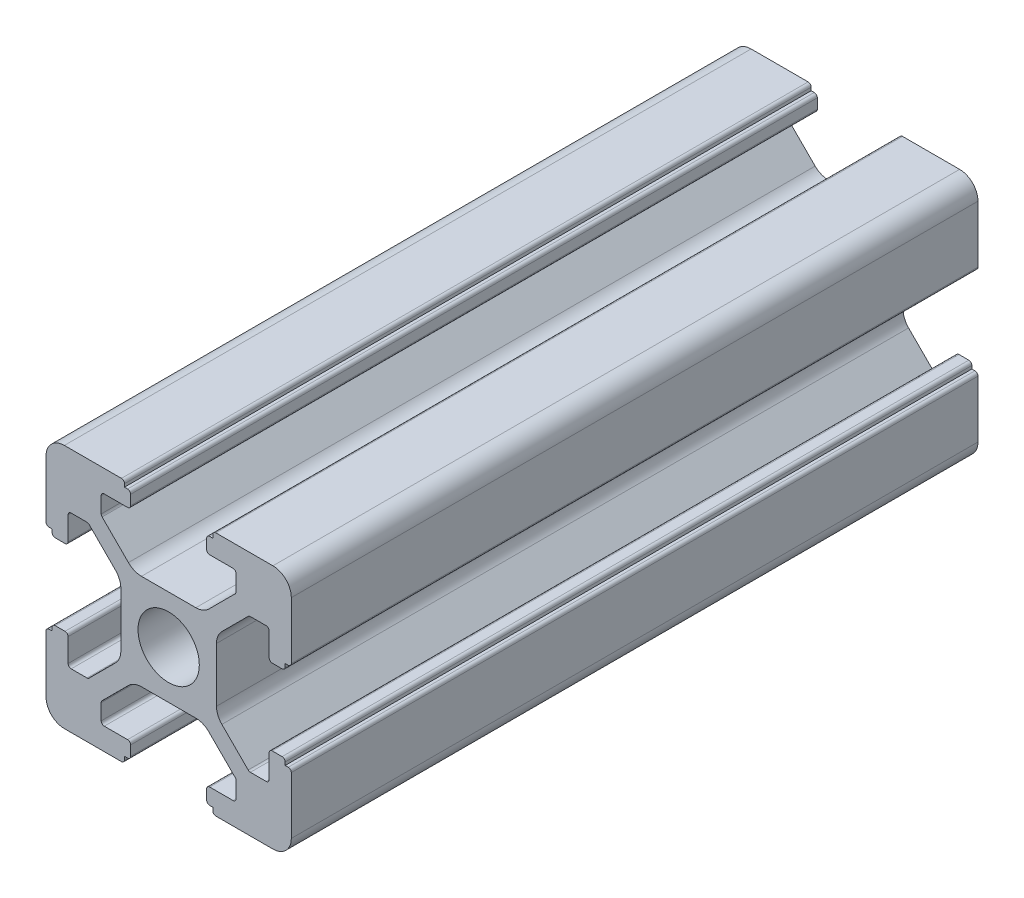
SolidWorks part; units mm, degrees
ref_plane "前视基准面" through (0, 0, 0) normal (0, 0, 1) x (1, 0, 0)
ref_plane "上视基准面" through (0, 0, 0) normal (0, 1, 0) x (1, 0, 0)
ref_plane "右视基准面" through (0, 0, 0) normal (1, 0, 0) x (0, 0, -1)
sketch "草图1" plane through (0, 0, 0) normal (0, 0, 1) x (1, 0, 0)
  line L0 (0, 0) -> (0, 5.5) construction
  line L1 (-8.5023, -10.0023) -> (-3.85, -10.0023)
  line L2 (-10.0023, -8.5023) -> (-10.0023, -3.85)
  line L3 (-8.5023, 10.0023) -> (-3.85, 10.0023)
  line L4 (10.0023, -8.5023) -> (10.0023, -3.85)
  line L5 (-10.0023, -10.0023) -> (10.0023, 10.0023) construction
  line L6 (-10.0023, 10.0023) -> (10.0023, -10.0023) construction
  line L7 (-2.218, -3.9) -> (2.218, -3.9)
  line L8 (-3.9, -2.218) -> (-3.9, 2.218)
  line L9 (-2.218, 3.9) -> (2.218, 3.9)
  line L10 (3.9, -2.218) -> (3.9, 2.218)
  line L11 (-3.9, -3.9) -> (3.9, 3.9) construction
  line L12 (-3.9, 3.9) -> (3.9, -3.9) construction
  line L13 (-5.25, -8.2) -> (-3.35, -8.2)
  line L14 (-8.2, -5.25) -> (-8.2, -3.35)
  line L15 (-5.25, 8.2) -> (-3.35, 8.2)
  line L16 (8.2, -5.25) -> (8.2, -3.35)
  line L17 (-8.2, -8.2) -> (8.2, 8.2) construction
  line L18 (-8.2, 8.2) -> (8.2, -8.2) construction
  line L19 (-7.95, 5.5) -> (-6.6642, 5.5)
  line L20 (0, 0) -> (5.5, 0) construction
  line L23 (-5.5, 7.95) -> (-5.5, 6.6642)
  line L26 (0, 0) -> (-0.5303, 0.5303)
  line L27 (3.2787, 4.3393) -> (5.4268, 6.4874)
  line L28 (0, 0) -> (0.5303, -0.5303)
  line L29 (5.5, 6.6642) -> (5.5, 7.95)
  line L30 (4.3393, 3.2787) -> (6.4874, 5.4268)
  line L31 (6.6642, 5.5) -> (7.95, 5.5)
  line L32 (4.3393, -3.2787) -> (6.4874, -5.4268)
  line L33 (3.2787, -4.3393) -> (5.4268, -6.4874)
  line L34 (-3.2787, -4.3393) -> (-5.4268, -6.4874)
  line L35 (-4.3393, -3.2787) -> (-6.4874, -5.4268)
  line L36 (-4.3393, 3.2787) -> (-6.4874, 5.4268)
  line L37 (-3.2787, 4.3393) -> (-5.4268, 6.4874)
  line L38 (3.1, -8.45) -> (3.1, -9.2523)
  line L39 (8.45, 3.1) -> (9.2523, 3.1)
  line L40 (-5.5, -6.6642) -> (-5.5, -7.95)
  line L41 (-6.6642, -5.5) -> (-7.95, -5.5)
  line L42 (5.5, -6.6642) -> (5.5, -7.95)
  line L43 (6.6642, -5.5) -> (7.95, -5.5)
  line L44 (9.2523, -3.1) -> (8.45, -3.1)
  line L46 (10.0023, 3.85) -> (10.0023, 8.5023)
  line L47 (8.2, 3.35) -> (8.2, 5.25)
  line L48 (-3.1, -9.2523) -> (-3.1, -8.45)
  line L49 (-8.45, -3.1) -> (-9.2523, -3.1)
  line L50 (-9.2523, 3.1) -> (-8.45, 3.1)
  line L51 (-3.1, 8.45) -> (-3.1, 9.2523)
  line L52 (3.1, 9.2523) -> (3.1, 8.45)
  line L53 (3.85, 10.0023) -> (8.5023, 10.0023)
  line L54 (3.35, 8.2) -> (5.25, 8.2)
  line L55 (-10.0023, 3.85) -> (-10.0023, 8.5023)
  line L56 (-8.2, 3.35) -> (-8.2, 5.25)
  line L57 (3.35, -8.2) -> (5.25, -8.2)
  line L58 (3.85, -10.0023) -> (8.5023, -10.0023)
  line L59 (9.7523, -3.6) -> (9.5023, -3.6)
  line L61 (9.7523, 3.6) -> (9.5023, 3.6)
  line L62 (9.5023, -3.6) -> (9.5023, -3.35)
  line L63 (3.6, -9.7523) -> (3.6, -9.5023)
  line L64 (3.35, -9.5023) -> (3.6, -9.5023)
  line L65 (9.5023, 3.35) -> (9.5023, 3.6)
  line L66 (-3.6, -9.5023) -> (-3.35, -9.5023)
  line L67 (-3.6, -9.7523) -> (-3.6, -9.5023)
  line L68 (-9.7523, -3.6) -> (-9.5023, -3.6)
  line L69 (-9.5023, -3.35) -> (-9.5023, -3.6)
  line L70 (-9.5023, 3.6) -> (-9.5023, 3.35)
  line L71 (-9.7523, 3.6) -> (-9.5023, 3.6)
  line L72 (-3.6, 9.7523) -> (-3.6, 9.5023)
  line L73 (-3.35, 9.5023) -> (-3.6, 9.5023)
  line L74 (3.6, 9.5023) -> (3.35, 9.5023)
  line L75 (3.6, 9.7523) -> (3.6, 9.5023)
  circle A0 centre (0, 0) radius 2.5
  arc A1 (10.0023, 8.5023) -> (8.5023, 10.0023) centre (8.5023, 8.5023) ccw
  arc A2 (8.5023, -10.0023) -> (10.0023, -8.5023) centre (8.5023, -8.5023) ccw
  arc A3 (-10.0023, -8.5023) -> (-8.5023, -10.0023) centre (-8.5023, -8.5023) ccw
  arc A4 (-10.0023, 8.5023) -> (-8.5023, 10.0023) centre (-8.5023, 8.5023) cw
  arc A5 (-9.5023, -3.35) -> (-9.2523, -3.1) centre (-9.2523, -3.35) cw
  arc A6 (-9.7523, -3.6) -> (-10.0023, -3.85) centre (-9.7523, -3.85) ccw
  arc A7 (-8.45, -3.1) -> (-8.2, -3.35) centre (-8.45, -3.35) cw
  arc A8 (-7.95, -5.5) -> (-8.2, -5.25) centre (-7.95, -5.25) cw
  arc A9 (-6.4874, -5.4268) -> (-6.6642, -5.5) centre (-6.6642, -5.25) cw
  arc A10 (-5.4268, -6.4874) -> (-5.5, -6.6642) centre (-5.25, -6.6642) ccw
  arc A11 (-5.5, -7.95) -> (-5.25, -8.2) centre (-5.25, -7.95) ccw
  arc A12 (-3.6, -9.7523) -> (-3.85, -10.0023) centre (-3.85, -9.7523) cw
  arc A13 (-3.35, -9.5023) -> (-3.1, -9.2523) centre (-3.35, -9.2523) ccw
  arc A14 (-3.1, -8.45) -> (-3.35, -8.2) centre (-3.35, -8.45) ccw
  arc A15 (3.1, -8.45) -> (3.35, -8.2) centre (3.35, -8.45) cw
  arc A16 (5.5, -7.95) -> (5.25, -8.2) centre (5.25, -7.95) cw
  arc A17 (5.4268, -6.4874) -> (5.5, -6.6642) centre (5.25, -6.6642) cw
  arc A18 (6.4874, -5.4268) -> (6.6642, -5.5) centre (6.6642, -5.25) ccw
  arc A19 (7.95, -5.5) -> (8.2, -5.25) centre (7.95, -5.25) ccw
  arc A20 (8.45, -3.1) -> (8.2, -3.35) centre (8.45, -3.35) ccw
  arc A21 (9.5023, -3.35) -> (9.2523, -3.1) centre (9.2523, -3.35) ccw
  arc A22 (9.7523, -3.6) -> (10.0023, -3.85) centre (9.7523, -3.85) cw
  arc A23 (3.35, -9.5023) -> (3.1, -9.2523) centre (3.35, -9.2523) cw
  arc A24 (3.6, -9.7523) -> (3.85, -10.0023) centre (3.85, -9.7523) ccw
  arc A25 (7.95, 5.5) -> (8.2, 5.25) centre (7.95, 5.25) cw
  arc A26 (8.2, 3.35) -> (8.45, 3.1) centre (8.45, 3.35) ccw
  arc A27 (9.5023, 3.35) -> (9.2523, 3.1) centre (9.2523, 3.35) cw
  arc A28 (9.7523, 3.6) -> (10.0023, 3.85) centre (9.7523, 3.85) ccw
  arc A29 (6.6642, 5.5) -> (6.4874, 5.4268) centre (6.6642, 5.25) ccw
  arc A30 (5.4268, 6.4874) -> (5.5, 6.6642) centre (5.25, 6.6642) ccw
  arc A31 (5.5, 7.95) -> (5.25, 8.2) centre (5.25, 7.95) ccw
  arc A32 (3.1, 8.45) -> (3.35, 8.2) centre (3.35, 8.45) ccw
  arc A33 (3.6, 9.7523) -> (3.85, 10.0023) centre (3.85, 9.7523) cw
  arc A34 (3.35, 9.5023) -> (3.1, 9.2523) centre (3.35, 9.2523) ccw
  arc A35 (-9.7523, 3.6) -> (-10.0023, 3.85) centre (-9.7523, 3.85) cw
  arc A36 (-9.5023, 3.35) -> (-9.2523, 3.1) centre (-9.2523, 3.35) ccw
  arc A37 (-8.45, 3.1) -> (-8.2, 3.35) centre (-8.45, 3.35) ccw
  arc A38 (-8.2, 5.25) -> (-7.95, 5.5) centre (-7.95, 5.25) cw
  arc A39 (-6.4874, 5.4268) -> (-6.6642, 5.5) centre (-6.6642, 5.25) ccw
  arc A40 (-5.4268, 6.4874) -> (-5.5, 6.6642) centre (-5.25, 6.6642) cw
  arc A41 (-5.5, 7.95) -> (-5.25, 8.2) centre (-5.25, 7.95) cw
  arc A42 (-3.1, 8.45) -> (-3.35, 8.2) centre (-3.35, 8.45) cw
  arc A43 (-3.1, 9.2523) -> (-3.35, 9.5023) centre (-3.35, 9.2523) ccw
  arc A44 (-3.6, 9.7523) -> (-3.85, 10.0023) centre (-3.85, 9.7523) ccw
  arc A45 (-4.3393, 3.2787) -> (-3.9, 2.218) centre (-5.4, 2.218) cw
  arc A46 (-3.2787, 4.3393) -> (-2.218, 3.9) centre (-2.218, 5.4) ccw
  arc A47 (3.2787, 4.3393) -> (2.218, 3.9) centre (2.218, 5.4) cw
  arc A48 (4.3393, 3.2787) -> (3.9, 2.218) centre (5.4, 2.218) ccw
  arc A49 (4.3393, -3.2787) -> (3.9, -2.218) centre (5.4, -2.218) cw
  arc A50 (3.2787, -4.3393) -> (2.218, -3.9) centre (2.218, -5.4) ccw
  arc A51 (-4.3393, -3.2787) -> (-3.9, -2.218) centre (-5.4, -2.218) ccw
  arc A52 (-2.218, -3.9) -> (-3.2787, -4.3393) centre (-2.218, -5.4) ccw
  point P0 (0, 0)
  point P7 (10.0023, 0)
  point P62 (0, 0)
  point P76 (0, 0)
  point P92 (-8.2, -5.5)
  point P99 (0, 0)
  point P106 (-5.5, -8.2)
  point P117 (5.5, -8.2)
  point P124 (8.2, -5.5)
  point P137 (8.2, 5.5)
  point P140 (8.2, 3.1)
  point P147 (6.5607, 5.5)
  point P152 (5.5, 8.2)
  point P167 (-8.2, 5.5)
  point P174 (-5.5, 8.2)
  dimension "D1" = 1.5
  dimension "D5" = 0.25
  dimension "D6" = 1.5
  dimension "D2" = 4
  dimension "D3" = 4
  dimension "D4" = 4
extrude "凸台-拉伸1" add sketch "草图1" along normal blind 56 contours A52 L7 A50 L33 A17 L42 A16 L57 A15 L38 A23 L64 L63 A24 L58 A2 L4 A22 L59 L62 A21 L44 A20 L16 A19 L43 A18 L32 A49 L10 A48 L30 A29 L31 A25 L47 A26 L39 A27 L65 L61 A28 L46 A1 L53 A33 L75 L74 A34 L52 A32
